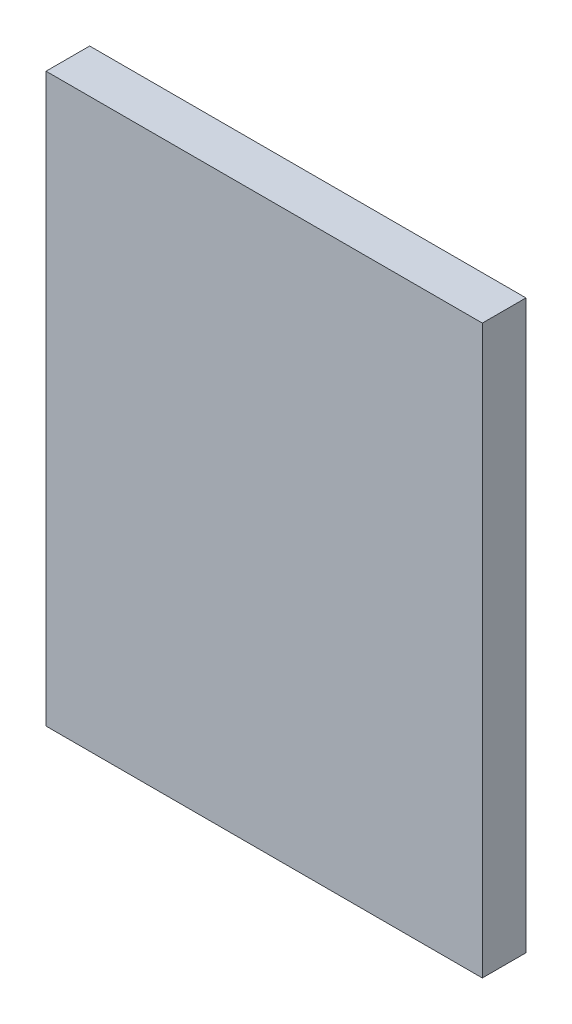
SolidWorks part; units mm, degrees
ref_plane "Front Plane" through (0, 0, 0) normal (0, 0, 1) x (1, 0, 0)
ref_plane "Top Plane" through (0, 0, 0) normal (0, 1, 0) x (1, 0, 0)
ref_plane "Right Plane" through (0, 0, 0) normal (1, 0, 0) x (0, 0, -1)
sketch "Sketch1" plane through (0, 0, 0) normal (0, 0, 1) x (1, 0, 0)
  line L1 (-95.25, -123.825) -> (95.25, -123.825)
  line L2 (-95.25, -123.825) -> (-95.25, 123.825)
  line L3 (-95.25, 123.825) -> (95.25, 123.825)
  line L4 (95.25, -123.825) -> (95.25, 123.825)
  line L5 (-95.25, -123.825) -> (95.25, 123.825) construction
  line L6 (-95.25, 123.825) -> (95.25, -123.825) construction
  point P0 (0, 0)
  dimension "D1" = 190.5
  dimension "D2" = 247.65
extrude "Boss-Extrude1" add sketch "Sketch1" along normal blind 19.05
